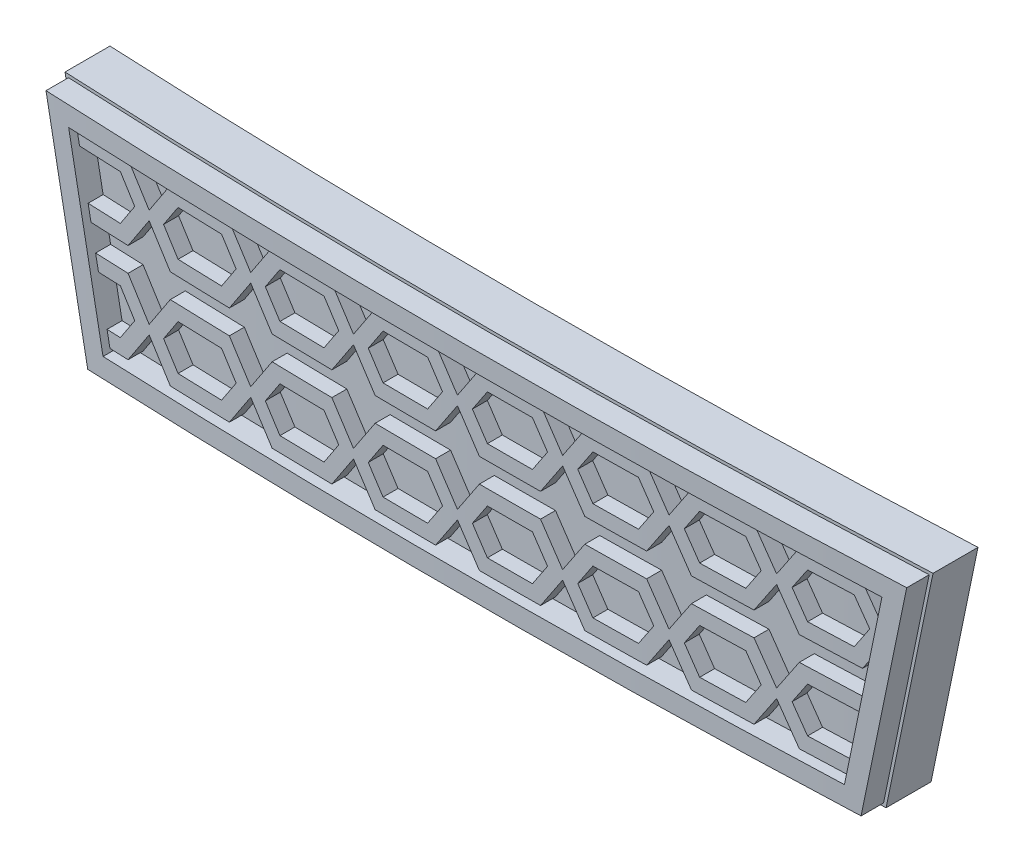
SolidWorks part; units mm, degrees
ref_plane "Front Plane" through (0, 0, 0) normal (0, 0, 1) x (1, 0, 0)
ref_plane "Top Plane" through (0, 0, 0) normal (0, 1, 0) x (1, 0, 0)
ref_plane "Right Plane" through (0, 0, 0) normal (1, 0, 0) x (0, 0, -1)
sketch "Sketch2" plane through (0, 0, 0) normal (0, 1, 0) x (1, 0, 0)
  line L3 (-73.1153, 2.6297) -> (-72.7519, 5.6076)
  line L4 (73.8847, 2.6297) -> (73.5213, 5.6076)
  arc A0 (-73.1153, 2.6297) -> (73.8847, 2.6297) centre (0.3847, 604.9793) ccw
  arc A1 (-72.7519, 5.6076) -> (73.5213, 5.6076) centre (0.3847, 604.9793) ccw
  dimension "D2" = 147
  dimension "D1" = 3
extrude "Boss-Extrude1" add sketch "Sketch2" along normal blind 25
sketch "Sketch4" plane through (0, 0, 0) normal (0, 0, 1) x (1, 0, 0)
  line L0 (0.3847, 25) -> (0, 0) construction
  line L2 (73.8847, 25) -> (-73.1153, 25) construction
  line L3 (-28.6888, 19.9982) -> (-25.6888, 4.9982)
  line L4 (-28.6888, 19.9982) -> (29.3112, 19.9982)
  line L5 (-25.6888, 4.9982) -> (26.3112, 4.9982)
  line L6 (29.3112, 19.9982) -> (26.3112, 4.9982)
  line L7 (-73.1153, 0) -> (73.8847, 0)
  line L8 (73.8847, 0) -> (73.8847, 25)
  line L9 (73.8847, 25) -> (-73.1153, 25)
  line L10 (-73.1153, 25) -> (-73.1153, 0)
  line L11 (-73.1153, 0) -> (73.8847, 0)
  line L12 (73.8847, 0) -> (73.8847, 25)
  line L13 (73.8847, 25) -> (-73.1153, 25)
  line L14 (-73.1153, 25) -> (-73.1153, 0)
  dimension "D2" = 58
  dimension "D3" = 15
  dimension "D4" = 29
  dimension "D1" = 0
extrude "Cut-Extrude1" cut sketch "Sketch4" against normal through all both and the other way through all
sketch "Sketch6" plane through (0, 0, 0) normal (0, 0, 1) x (1, 0, 0)
  line L10 (0.3112, 19.9982) -> (0.3112, 4.9982) construction
  line L11 (29.3112, 19.9982) -> (-28.6888, 19.9982) construction
  line L12 (-25.6888, 4.9982) -> (26.3112, 4.9982) construction
  line L13 (-25.6591, 12.4982) -> (26.2815, 12.4982) construction
  line L14 (25.0815, 6.4982) -> (27.4815, 18.4982)
  line L15 (-24.4591, 6.4982) -> (25.0815, 6.4982)
  line L16 (-26.8591, 18.4982) -> (-24.4591, 6.4982)
  line L17 (27.4815, 18.4982) -> (-26.8591, 18.4982)
  line L18 (25.8841, 10.5113) -> (26.0379, 11.2805)
  line L20 (-26.8198, 18.3017) -> (-26.6198, 17.3017)
  line L61 (-26.8198, 18.3017) -> (-23.2382, 18.3017)
  line L62 (-21.7733, 16.1044) -> (-23.2382, 18.3017)
  line L63 (-23.2382, 13.3017) -> (-21.7733, 15.4989)
  line L64 (-23.2382, 13.3017) -> (-25.8198, 13.3017)
  line L67 (-20.3085, 18.3017) -> (-16.2382, 18.3017)
  line L68 (-14.7733, 16.1044) -> (-16.2382, 18.3017)
  line L69 (-16.2382, 13.3017) -> (-14.7733, 15.4989)
  line L70 (-16.2382, 13.3017) -> (-20.3085, 13.3017)
  line L71 (-20.3085, 13.3017) -> (-21.7733, 15.4989)
  line L72 (-21.7733, 16.1044) -> (-20.3085, 18.3017)
  line L73 (-13.3085, 18.3017) -> (-9.2382, 18.3017)
  line L74 (-7.7733, 16.1044) -> (-9.2382, 18.3017)
  line L75 (-9.2382, 13.3017) -> (-7.7733, 15.4989)
  line L76 (-9.2382, 13.3017) -> (-13.3085, 13.3017)
  line L77 (-13.3085, 13.3017) -> (-14.7733, 15.4989)
  line L78 (-14.7733, 16.1044) -> (-13.3085, 18.3017)
  line L79 (-6.3085, 18.3017) -> (-2.2382, 18.3017)
  line L80 (-2.2382, 13.3017) -> (-0.7733, 15.4989)
  line L81 (-2.2382, 13.3017) -> (-6.3085, 13.3017)
  line L82 (-6.3085, 13.3017) -> (-7.7733, 15.4989)
  line L83 (-7.7733, 16.1044) -> (-6.3085, 18.3017)
  line L84 (0.6915, 18.3017) -> (4.7618, 18.3017)
  line L85 (6.2267, 16.1044) -> (4.7618, 18.3017)
  line L86 (4.7618, 13.3017) -> (6.2267, 15.4989)
  line L87 (4.7618, 13.3017) -> (0.6915, 13.3017)
  line L88 (0.6915, 13.3017) -> (-0.7733, 15.4989)
  line L89 (-0.7733, 16.1044) -> (0.6915, 18.3017)
  line L90 (7.6915, 18.3017) -> (11.7618, 18.3017)
  line L91 (13.2267, 16.1044) -> (11.7618, 18.3017)
  line L92 (11.7618, 13.3017) -> (13.2267, 15.4989)
  line L93 (11.7618, 13.3017) -> (7.6915, 13.3017)
  line L94 (7.6915, 13.3017) -> (6.2267, 15.4989)
  line L95 (6.2267, 16.1044) -> (7.6915, 18.3017)
  line L96 (14.6915, 18.3017) -> (18.7618, 18.3017)
  line L97 (20.2267, 16.1044) -> (18.7618, 18.3017)
  line L98 (18.7618, 13.3017) -> (20.2267, 15.4989)
  line L99 (18.7618, 13.3017) -> (14.6915, 13.3017)
  line L100 (14.6915, 13.3017) -> (13.2267, 15.4989)
  line L101 (13.2267, 16.1044) -> (14.6915, 18.3017)
  line L102 (21.6915, 18.3017) -> (25.7618, 18.3017)
  line L103 (27.0544, 16.3628) -> (25.7618, 18.3017)
  line L104 (25.7618, 13.3017) -> (26.7337, 14.7595)
  line L105 (25.7618, 13.3017) -> (21.6915, 13.3017)
  line L106 (21.6915, 13.3017) -> (20.2267, 15.4989)
  line L107 (20.2267, 16.1044) -> (21.6915, 18.3017)
  line L120 (-0.7733, 16.1044) -> (-2.2382, 18.3017)
  line L122 (-26.6198, 17.3017) -> (-23.7733, 17.3017)
  line L123 (25.7618, 11.6947) -> (26.0379, 11.2805)
  line L124 (25.7618, 11.6947) -> (21.6915, 11.6947)
  line L125 (21.6915, 6.6947) -> (25.1208, 6.6947)
  line L126 (20.2267, 8.8919) -> (21.6915, 6.6947)
  line L127 (21.6915, 11.6947) -> (20.2267, 9.4975)
  line L128 (20.2267, 8.8919) -> (18.7618, 6.6947)
  line L129 (18.7618, 11.6947) -> (20.2267, 9.4975)
  line L130 (18.7618, 11.6947) -> (14.6915, 11.6947)
  line L131 (14.6915, 6.6947) -> (18.7618, 6.6947)
  line L132 (13.2267, 8.8919) -> (14.6915, 6.6947)
  line L133 (14.6915, 11.6947) -> (13.2267, 9.4975)
  line L134 (13.2267, 8.8919) -> (11.7618, 6.6947)
  line L135 (11.7618, 11.6947) -> (13.2267, 9.4975)
  line L136 (11.7618, 11.6947) -> (7.6915, 11.6947)
  line L137 (7.6915, 6.6947) -> (11.7618, 6.6947)
  line L138 (6.2267, 8.8919) -> (7.6915, 6.6947)
  line L139 (7.6915, 11.6947) -> (6.2267, 9.4975)
  line L140 (4.7618, 11.6947) -> (6.2267, 9.4975)
  line L141 (6.2267, 8.8919) -> (4.7618, 6.6947)
  line L142 (0.6915, 6.6947) -> (4.7618, 6.6947)
  line L143 (4.7618, 11.6947) -> (0.6915, 11.6947)
  line L144 (0.6915, 11.6947) -> (-0.7733, 9.4975)
  line L145 (-0.7733, 8.8919) -> (0.6915, 6.6947)
  line L146 (-0.7733, 8.8919) -> (-2.2382, 6.6947)
  line L147 (-2.2382, 11.6947) -> (-0.7733, 9.4975)
  line L148 (-2.2382, 11.6947) -> (-6.3085, 11.6947)
  line L149 (-6.3085, 6.6947) -> (-2.2382, 6.6947)
  line L150 (-6.3085, 11.6947) -> (-7.7733, 9.4975)
  line L151 (-7.7733, 8.8919) -> (-6.3085, 6.6947)
  line L152 (-7.7733, 8.8919) -> (-9.2382, 6.6947)
  line L153 (-9.2382, 11.6947) -> (-7.7733, 9.4975)
  line L154 (-13.3085, 6.6947) -> (-9.2382, 6.6947)
  line L155 (-9.2382, 11.6947) -> (-13.3085, 11.6947)
  line L156 (-13.3085, 11.6947) -> (-14.7733, 9.4975)
  line L157 (-14.7733, 8.8919) -> (-13.3085, 6.6947)
  line L158 (-14.7733, 8.8919) -> (-16.2382, 6.6947)
  line L159 (-16.2382, 11.6947) -> (-14.7733, 9.4975)
  line L160 (-16.2382, 11.6947) -> (-20.3085, 11.6947)
  line L161 (-20.3085, 6.6947) -> (-16.2382, 6.6947)
  line L162 (-21.7733, 8.8919) -> (-20.3085, 6.6947)
  line L163 (-20.3085, 11.6947) -> (-21.7733, 9.4975)
  line L164 (-23.2382, 11.6947) -> (-21.7733, 9.4975)
  line L165 (-23.2382, 11.6947) -> (-25.4984, 11.6947)
  line L166 (-24.4984, 6.6947) -> (-23.2382, 6.6947)
  line L167 (-21.7733, 8.8919) -> (-23.2382, 6.6947)
  line L168 (-25.8198, 14.3017) -> (-26.0198, 14.3017)
  line L169 (-26.0198, 14.3017) -> (-25.8198, 13.3017)
  line L170 (-19.7733, 17.3017) -> (-16.7733, 17.3017)
  line L173 (-12.7733, 17.3017) -> (-9.7733, 17.3017)
  line L174 (-8.7733, 15.8017) -> (-9.7733, 17.3017)
  line L176 (-5.7733, 17.3017) -> (-2.7733, 17.3017)
  line L179 (1.2267, 17.3017) -> (4.2267, 17.3017)
  line L180 (5.2267, 15.8017) -> (4.2267, 17.3017)
  line L182 (8.2267, 17.3017) -> (11.2267, 17.3017)
  line L183 (12.2267, 15.8017) -> (11.2267, 17.3017)
  line L185 (15.2267, 17.3017) -> (18.2267, 17.3017)
  line L186 (19.2267, 15.8017) -> (18.2267, 17.3017)
  line L188 (22.2267, 17.3017) -> (25.2267, 17.3017)
  line L189 (26.2223, 15.8081) -> (25.2267, 17.3017)
  line L190 (25.2267, 14.3017) -> (25.9017, 15.3142)
  line L191 (25.2267, 14.3017) -> (22.2267, 14.3017)
  line L192 (22.2267, 14.3017) -> (21.2267, 15.8017)
  line L193 (18.2267, 14.3017) -> (19.2267, 15.8017)
  line L194 (18.2267, 14.3017) -> (15.2267, 14.3017)
  line L195 (15.2267, 14.3017) -> (14.2267, 15.8017)
  line L196 (11.2267, 14.3017) -> (12.2267, 15.8017)
  line L197 (11.2267, 14.3017) -> (8.2267, 14.3017)
  line L198 (8.2267, 14.3017) -> (7.2267, 15.8017)
  line L199 (4.2267, 14.3017) -> (5.2267, 15.8017)
  line L200 (4.2267, 14.3017) -> (1.2267, 14.3017)
  line L201 (1.2267, 14.3017) -> (0.2267, 15.8017)
  line L202 (-2.7733, 14.3017) -> (-1.7733, 15.8017)
  line L203 (-2.7733, 14.3017) -> (-5.7733, 14.3017)
  line L204 (-5.7733, 14.3017) -> (-6.7733, 15.8017)
  line L205 (-9.7733, 14.3017) -> (-8.7733, 15.8017)
  line L206 (-9.7733, 14.3017) -> (-12.7733, 14.3017)
  line L207 (-12.7733, 14.3017) -> (-13.7733, 15.8017)
  line L208 (-16.7733, 14.3017) -> (-15.7733, 15.8017)
  line L209 (-16.7733, 14.3017) -> (-19.7733, 14.3017)
  line L210 (-19.7733, 14.3017) -> (-20.7733, 15.8017)
  line L211 (-23.7733, 14.3017) -> (-22.7733, 15.8017)
  line L212 (-23.7733, 14.3017) -> (-25.8198, 14.3017)
  line L213 (25.9017, 15.3142) -> (26.2223, 15.8081)
  line L214 (25.7618, 10.6947) -> (22.2267, 10.6947)
  line L215 (22.2267, 10.6947) -> (21.2267, 9.1947)
  line L216 (18.2267, 10.6947) -> (19.2267, 9.1947)
  line L217 (18.2267, 10.6947) -> (15.2267, 10.6947)
  line L218 (15.2267, 10.6947) -> (14.2267, 9.1947)
  line L219 (11.2267, 10.6947) -> (12.2267, 9.1947)
  line L220 (11.2267, 10.6947) -> (8.2267, 10.6947)
  line L221 (8.2267, 10.6947) -> (7.2267, 9.1947)
  line L222 (4.2267, 10.6947) -> (5.2267, 9.1947)
  line L223 (4.2267, 10.6947) -> (1.2267, 10.6947)
  line L224 (1.2267, 10.6947) -> (0.2267, 9.1947)
  line L225 (-2.7733, 10.6947) -> (-1.7733, 9.1947)
  line L226 (-2.7733, 10.6947) -> (-5.7733, 10.6947)
  line L227 (-5.7733, 10.6947) -> (-6.7733, 9.1947)
  line L228 (-9.7733, 10.6947) -> (-8.7733, 9.1947)
  line L229 (-9.7733, 10.6947) -> (-12.7733, 10.6947)
  line L230 (-12.7733, 10.6947) -> (-13.7733, 9.1947)
  line L231 (-16.7733, 10.6947) -> (-15.7733, 9.1947)
  line L232 (-16.7733, 10.6947) -> (-19.7733, 10.6947)
  line L233 (-19.7733, 10.6947) -> (-20.7733, 9.1947)
  line L234 (-23.7733, 10.6947) -> (-22.7733, 9.1947)
  line L235 (-23.7733, 10.6947) -> (-25.2984, 10.6947)
  line L236 (-24.4984, 7.6947) -> (-23.7733, 7.6947)
  line L237 (-22.7733, 9.1947) -> (-23.7733, 7.6947)
  line L238 (-20.7733, 9.1947) -> (-19.7733, 7.6947)
  line L239 (-19.7733, 7.6947) -> (-16.7733, 7.6947)
  line L240 (-15.7733, 9.1947) -> (-16.7733, 7.6947)
  line L241 (-13.7733, 9.1947) -> (-12.7733, 7.6947)
  line L242 (-12.7733, 7.6947) -> (-9.7733, 7.6947)
  line L243 (-8.7733, 9.1947) -> (-9.7733, 7.6947)
  line L244 (-6.7733, 9.1947) -> (-5.7733, 7.6947)
  line L245 (-5.7733, 7.6947) -> (-2.7733, 7.6947)
  line L246 (-1.7733, 9.1947) -> (-2.7733, 7.6947)
  line L247 (-22.7733, 15.8017) -> (-23.7733, 17.3017)
  line L248 (1.2267, 7.6947) -> (4.2267, 7.6947)
  line L249 (-7.7733, 10.6947) -> (-9.7733, 7.6947) construction
  line L250 (0.2267, 9.1947) -> (1.2267, 7.6947)
  line L251 (8.2267, 7.6947) -> (11.2267, 7.6947)
  line L252 (12.2267, 9.1947) -> (11.2267, 7.6947)
  line L253 (7.2267, 9.1947) -> (8.2267, 7.6947)
  line L254 (15.2267, 7.6947) -> (18.2267, 7.6947)
  line L255 (19.2267, 9.1947) -> (18.2267, 7.6947)
  line L256 (21.2267, 9.1947) -> (22.2267, 7.6947)
  line L257 (22.2267, 7.6947) -> (25.1208, 7.6947)
  line L258 (25.7618, 10.6947) -> (25.8841, 10.5113)
  line L259 (25.1208, 7.6947) -> (25.3708, 7.9447)
  line L260 (26.7337, 14.7595) -> (27.0544, 16.3628)
  line L261 (25.3708, 7.9447) -> (25.1208, 6.6947)
  line L262 (14.2267, 9.1947) -> (15.2267, 7.6947)
  line L263 (20.2267, 10.6947) -> (22.2267, 7.6947) construction
  line L264 (20.2267, 10.6947) -> (18.2267, 7.6947) construction
  line L265 (22.2267, 10.6947) -> (20.2267, 7.6947) construction
  line L266 (18.2267, 10.6947) -> (20.2267, 7.6947) construction
  line L267 (13.2267, 10.6947) -> (11.2267, 7.6947) construction
  line L268 (13.2267, 10.6947) -> (15.2267, 7.6947) construction
  line L269 (15.2267, 10.6947) -> (13.2267, 7.6947) construction
  line L270 (11.2267, 10.6947) -> (13.2267, 7.6947) construction
  line L271 (1.2267, 10.6947) -> (-0.7733, 7.6947) construction
  line L272 (6.2267, 10.6947) -> (8.2267, 7.6947) construction
  line L273 (5.2267, 9.1947) -> (4.2267, 7.6947)
  line L274 (8.2267, 10.6947) -> (6.2267, 7.6947) construction
  line L275 (4.2267, 10.6947) -> (6.2267, 7.6947) construction
  line L276 (-2.7733, 10.6947) -> (-0.7733, 7.6947) construction
  line L277 (6.2267, 10.6947) -> (4.2267, 7.6947) construction
  line L278 (-0.7733, 10.6947) -> (1.2267, 7.6947) construction
  line L279 (-0.7733, 10.6947) -> (-2.7733, 7.6947) construction
  line L280 (-7.7733, 10.6947) -> (-5.7733, 7.6947) construction
  line L281 (-9.7733, 10.6947) -> (-7.7733, 7.6947) construction
  line L282 (-5.7733, 10.6947) -> (-7.7733, 7.6947) construction
  line L283 (-14.7733, 10.6947) -> (-16.7733, 7.6947) construction
  line L284 (-14.7733, 10.6947) -> (-12.7733, 7.6947) construction
  line L285 (-21.7733, 10.6947) -> (-23.7733, 7.6947) construction
  line L286 (-16.7733, 10.6947) -> (-14.7733, 7.6947) construction
  line L287 (-21.7733, 10.6947) -> (-19.7733, 7.6947) construction
  line L288 (-12.7733, 10.6947) -> (-14.7733, 7.6947) construction
  line L289 (-23.7733, 10.6947) -> (-21.7733, 7.6947) construction
  line L290 (-19.7733, 10.6947) -> (-21.7733, 7.6947) construction
  line L291 (-23.7733, 14.3017) -> (-21.7733, 17.3017) construction
  line L292 (-20.7733, 15.8017) -> (-19.7733, 17.3017)
  line L293 (-21.7733, 14.3017) -> (-23.7733, 17.3017) construction
  line L294 (-25.4984, 11.6947) -> (-25.2984, 10.6947)
  line L295 (-21.7733, 14.3017) -> (-19.7733, 17.3017) construction
  line L296 (-26.8198, 17.3017) -> (-23.7733, 17.3017) construction
  line L297 (-19.7733, 14.3017) -> (-21.7733, 17.3017) construction
  line L298 (-24.4984, 7.6947) -> (-24.6984, 7.6947)
  line L299 (-23.7733, 10.6947) -> (-25.4984, 10.6947) construction
  line L300 (-24.6984, 7.6947) -> (-24.4984, 6.6947)
  line L301 (-15.7733, 15.8017) -> (-16.7733, 17.3017)
  line L302 (-16.7733, 14.3017) -> (-14.7733, 17.3017) construction
  line L303 (-12.7733, 14.3017) -> (-14.7733, 17.3017) construction
  line L304 (-13.7733, 15.8017) -> (-12.7733, 17.3017)
  line L305 (-14.7733, 14.3017) -> (-16.7733, 17.3017) construction
  line L306 (21.2267, 15.8017) -> (22.2267, 17.3017)
  line L307 (-14.7733, 14.3017) -> (-12.7733, 17.3017) construction
  line L308 (22.2267, 14.3017) -> (20.2267, 17.3017) construction
  line L309 (18.2267, 14.3017) -> (20.2267, 17.3017) construction
  line L310 (7.2267, 15.8017) -> (8.2267, 17.3017)
  line L311 (20.2267, 14.3017) -> (22.2267, 17.3017) construction
  line L312 (20.2267, 14.3017) -> (18.2267, 17.3017) construction
  line L313 (14.2267, 15.8017) -> (15.2267, 17.3017)
  line L314 (15.2267, 14.3017) -> (13.2267, 17.3017) construction
  line L315 (8.2267, 14.3017) -> (6.2267, 17.3017) construction
  line L316 (13.2267, 14.3017) -> (15.2267, 17.3017) construction
  line L317 (13.2267, 14.3017) -> (11.2267, 17.3017) construction
  line L318 (11.2267, 14.3017) -> (13.2267, 17.3017) construction
  line L319 (4.2267, 14.3017) -> (6.2267, 17.3017) construction
  line L320 (-1.7733, 15.8017) -> (-2.7733, 17.3017)
  line L321 (6.2267, 14.3017) -> (8.2267, 17.3017) construction
  line L322 (6.2267, 14.3017) -> (4.2267, 17.3017) construction
  line L323 (0.2267, 15.8017) -> (1.2267, 17.3017)
  line L324 (1.2267, 14.3017) -> (-0.7733, 17.3017) construction
  line L325 (-2.7733, 14.3017) -> (-0.7733, 17.3017) construction
  line L326 (-0.7733, 14.3017) -> (-2.7733, 17.3017) construction
  line L327 (-6.7733, 15.8017) -> (-5.7733, 17.3017)
  line L328 (-0.7733, 14.3017) -> (1.2267, 17.3017) construction
  line L329 (-9.7733, 14.3017) -> (-7.7733, 17.3017) construction
  line L330 (-5.7733, 14.3017) -> (-7.7733, 17.3017) construction
  line L332 (-7.7733, 14.3017) -> (-5.7733, 17.3017) construction
  line L333 (-7.7733, 14.3017) -> (-9.7733, 17.3017) construction
  dimension "D1" = 1.5
  dimension "D2" = 1
  dimension "D3" = 1
extrude "Boss-Extrude2" add sketch "Sketch6" along normal mid plane 20
sketch "Sketch7" plane through (0, 19.9982, 0) normal (0, 1, 0) x (1, 0, 0)
  line L0 (-28.6888, 1.8623) -> (-28.6888, 14.0634)
  line L1 (-28.6888, 14.0634) -> (29.3112, 14.0634)
  line L2 (29.3112, 14.0634) -> (29.3112, 1.8552)
  arc A0 (-28.6888, 1.8623) -> (29.3112, 1.8552) centre (0.3847, 604.9793) ccw construction
  arc A1 (-28.6888, 1.8623) -> (29.3112, 1.8552) centre (0.3847, 604.9793) ccw
extrude "Cut-Extrude2" cut sketch "Sketch7" against normal through all
sketch "Sketch8" plane through (0, 19.9982, 0) normal (0, 1, 0) x (1, 0, 0)
  line L2 (-28.7367, -2.14) -> (-29.2502, -12.8452)
  line L3 (-29.2502, -12.8452) -> (31.1742, -11.7792)
  line L4 (31.1742, -11.7792) -> (29.3588, -2.1471)
  arc A2 (-28.7367, -2.14) -> (29.3588, -2.1471) centre (0.3847, 604.9793) ccw
extrude "Cut-Extrude3" cut sketch "Sketch8" against normal through all
sketch "Sketch9" plane through (0, 0, 0) normal (0, 0, 1) x (1, 0, 0)
  line L10 (27.4815, 18.4982) -> (-26.8591, 18.4982)
  line L11 (-26.8591, 18.4982) -> (-24.4591, 6.4982)
  line L12 (-24.4591, 6.4982) -> (25.0815, 6.4982)
  line L13 (25.0815, 6.4982) -> (27.4815, 18.4982)
  line L14 (-25.5249, 5.1982) -> (26.1472, 5.1982)
  line L15 (-28.4449, 19.7982) -> (-25.5249, 5.1982)
  line L16 (29.0672, 19.7982) -> (-28.4449, 19.7982)
  line L17 (26.1472, 5.1982) -> (29.0672, 19.7982)
  line L18 (-25.5249, 5.1982) -> (26.1472, 5.1982)
  line L19 (-28.4449, 19.7982) -> (-25.5249, 5.1982)
  line L20 (29.0672, 19.7982) -> (-28.4449, 19.7982)
  line L21 (26.1472, 5.1982) -> (29.0672, 19.7982)
  dimension "D1" = 0.2
  dimension "D2" = 1.3
extrude "Boss-Extrude3" add sketch "Sketch9" along normal mid plane 10
sketch "Sketch11" plane through (0, 19.9982, 0) normal (0, 1, 0) x (1, 0, 0)
  line L0 (-28.6888, 1.8623) -> (-28.6888, 6.0659)
  line L1 (-28.6888, 6.0659) -> (29.3112, 6.0659)
  line L2 (29.3112, 6.0659) -> (29.3112, 1.8552)
  line L5 (-28.7607, -2.6395) -> (-28.9427, -6.4332)
  line L6 (-28.9427, -6.4332) -> (29.3827, -6.4332)
  line L7 (29.3827, -6.4332) -> (29.3827, -2.6465)
  arc A0 (-28.6888, 1.8623) -> (29.3112, 1.8552) centre (0.3847, 604.9793) ccw construction
  arc A1 (-28.6888, 1.8623) -> (29.3112, 1.8552) centre (0.3847, 604.9793) ccw
  arc A4 (-28.7607, -2.6395) -> (29.3827, -2.6465) centre (0.3847, 604.9793) ccw
extrude "Cut-Extrude4" cut sketch "Sketch11" against normal through all
